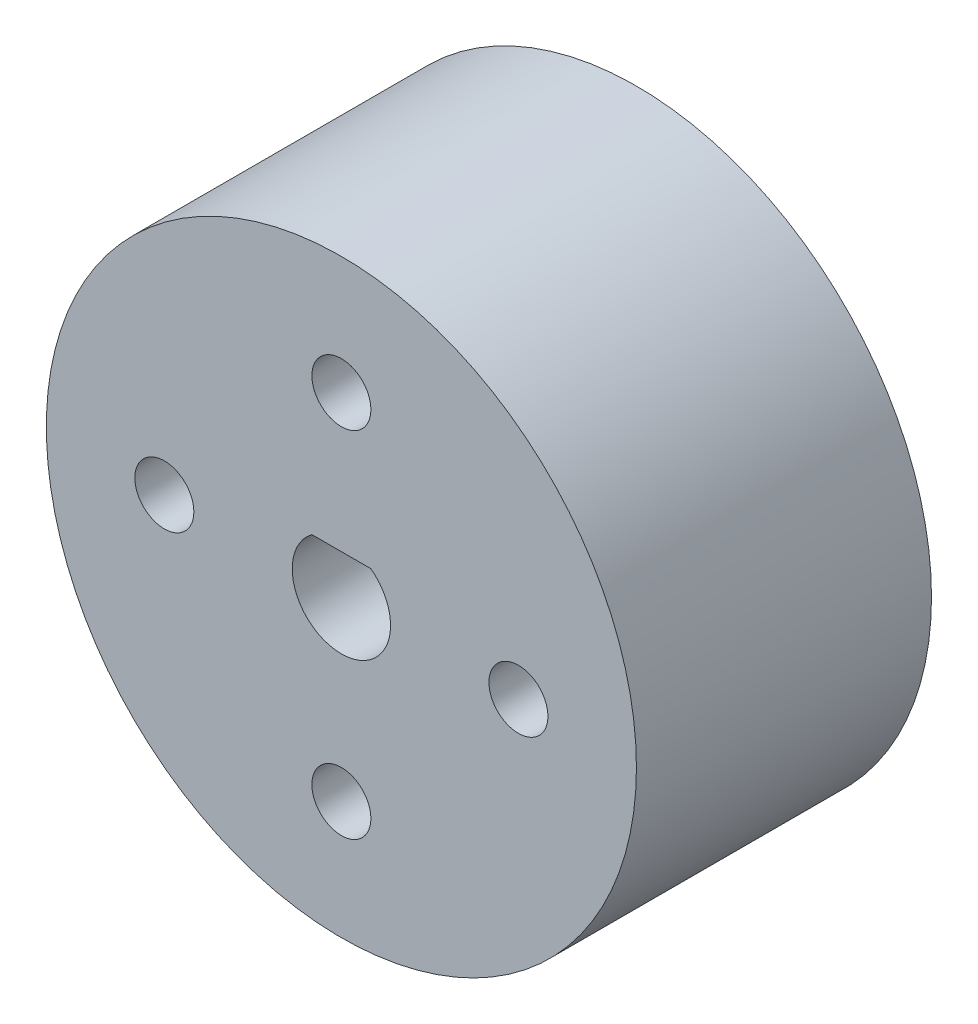
SolidWorks part; units mm, degrees
ref_plane "Front Plane" through (0, 0, 0) normal (0, 0, 1) x (1, 0, 0)
ref_plane "Top Plane" through (0, 0, 0) normal (0, 1, 0) x (1, 0, 0)
ref_plane "Right Plane" through (0, 0, 0) normal (1, 0, 0) x (0, 0, -1)
sketch "Sketch1" plane through (0, 0, 0) normal (0, 0, 1) x (1, 0, 0)
  circle A0 centre (0, 0) radius 15
  dimension "D1" = 30
extrude "Boss-Extrude1" add sketch "Sketch1" along normal blind 15
sketch "Sketch2" plane through (0, 0, 15) normal (0, 0, 1) x (1, 0, 0)
  line L0 (-2.5, 0) -> (2.5, 0) construction
  line L1 (-1.5, 2) -> (1.5, 2) construction
  line L2 (-1.5, 2) -> (1.5, 2)
  arc A0 (-1.5, 2) -> (1.5, 2) centre (0, 0) ccw
  dimension "D1" = 5
  dimension "D2" = 3
extrude "Cut-Extrude1" cut sketch "Sketch2" against normal blind 15
sketch "Sketch3" plane through (0, 0, 15) normal (0, 0, 1) x (1, 0, 0)
  line L0 (0, 0) -> (0, 11.5194) construction
  circle A0 centre (0, 9) radius 1.5
  circle A1 centre (9, 0) radius 1.5
  circle A2 centre (0, -9) radius 1.5
  circle A3 centre (-9, 0) radius 1.5
  dimension "D1" = 3
  dimension "D2" = 9
  dimension "D3" = 4
extrude "Cut-Extrude2" cut sketch "Sketch3" against normal blind 15
